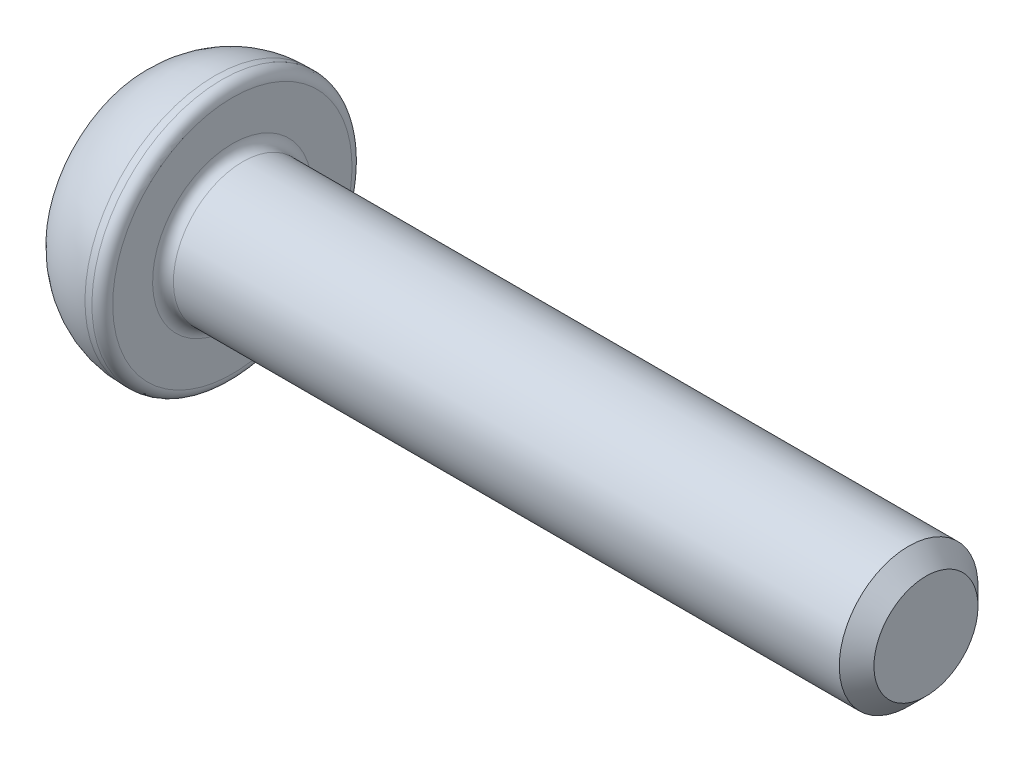
SolidWorks part; units mm, degrees
ref_plane "Спереди" through (0, 0, 0) normal (0, 0, 1) x (1, 0, 0)
ref_plane "Сверху" through (0, 0, 0) normal (0, 1, 0) x (1, 0, 0)
ref_plane "Справа" through (0, 0, 0) normal (1, 0, 0) x (0, 0, -1)
sketch "Эскиз1" plane through (0, 0, 0) normal (0, 0, 1) x (1, 0, 0)
  line L0 (0, 0) -> (0, 2.875)
  line L1 (2, 3.75) -> (2.5, 3.75)
  line L2 (2.5, 3.75) -> (2.5, 2)
  line L3 (2.5, 2) -> (22.5, 2)
  line L4 (22.5, 2) -> (22.5, 0)
  line L5 (22.5, 0) -> (0, 0) construction
  line L6 (0, 0) -> (22.5, 0)
  arc A0 (0, 2.875) -> (2, 3.75) centre (2, 1.0268) cw
  point P9 (2.5, 2.875)
  dimension "D1" = 0.5
  dimension "D2" = 4
  dimension "D3" = 7.5
  dimension "D5" = 2.5
  dimension "D6" = 20
revolve "Повернуть1" add sketch "Эскиз1" angle 360 about L5
cosmetic thread "Условное изображение резьбы1" parameters "D2"=3.22
sketch "Эскиз2" plane through (0, 0, 0) normal (-1, 0, 0) x (0, 0, 1)
  line L1 (0.7217, 1.25) -> (-0.7217, 1.25)
  line L2 (-0.7217, 1.25) -> (-1.4434, 0)
  line L3 (-1.4434, 0) -> (-0.7217, -1.25)
  line L4 (-0.7217, -1.25) -> (0.7217, -1.25)
  line L5 (0.7217, -1.25) -> (1.4434, 0)
  line L6 (1.4434, 0) -> (0.7217, 1.25)
  circle A0 centre (0, 0) radius 1.25 construction
  dimension "D1" = 2.5
extrude "Вырез-Вытянуть1" cut sketch "Эскиз2" against normal blind 1.5
fillet "Скругление1" radius 0.3 2 edges at (2.5, 2, 0) (2.5, 3.75, 0)
chamfer "Фаска1" distance 0.5 angle 45 1 edges at (22.5, 2, 0)
